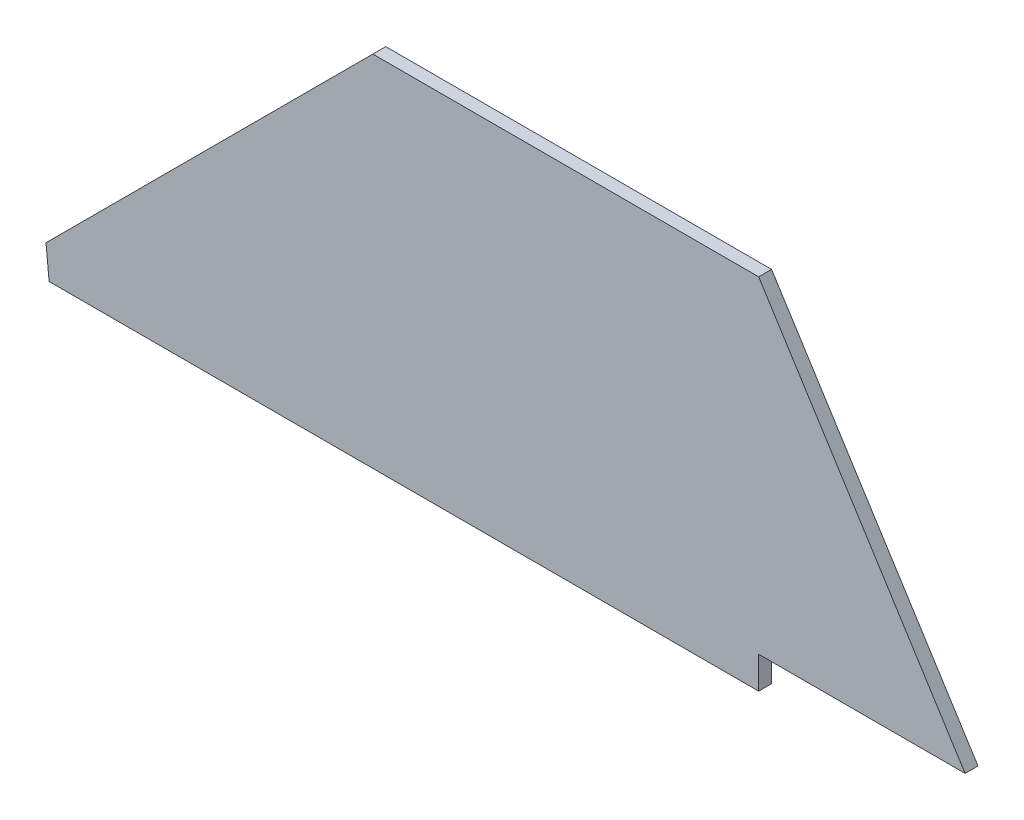
SolidWorks part; units mm, degrees
ref_plane "Front Plane" through (0, 0, 0) normal (0, 0, 1) x (1, 0, 0)
ref_plane "Top Plane" through (0, 0, 0) normal (0, 1, 0) x (1, 0, 0)
ref_plane "Right Plane" through (0, 0, 0) normal (1, 0, 0) x (0, 0, -1)
sketch "Sketch1" plane through (0, 0, 0) normal (0, 0, 1) x (1, 0, 0)
  line L8 (0, 0) -> (174.625, 0)
  line L9 (174.625, 0) -> (174.625, 7.874)
  line L10 (174.625, 7.874) -> (225.425, 7.874)
  line L11 (225.425, 7.874) -> (174.625, 88.3067)
  line L12 (174.625, 88.3067) -> (79.6724, 88.3067)
  line L13 (79.6724, 88.3067) -> (-0.7603, 7.874)
  line L14 (-0.7603, 7.874) -> (0, 0)
  dimension "D1" = 174.625
  dimension "D2" = 7.874
  dimension "D3" = 50.8
extrude "Boss-Extrude1" add sketch "Sketch1" along normal blind 3.175
